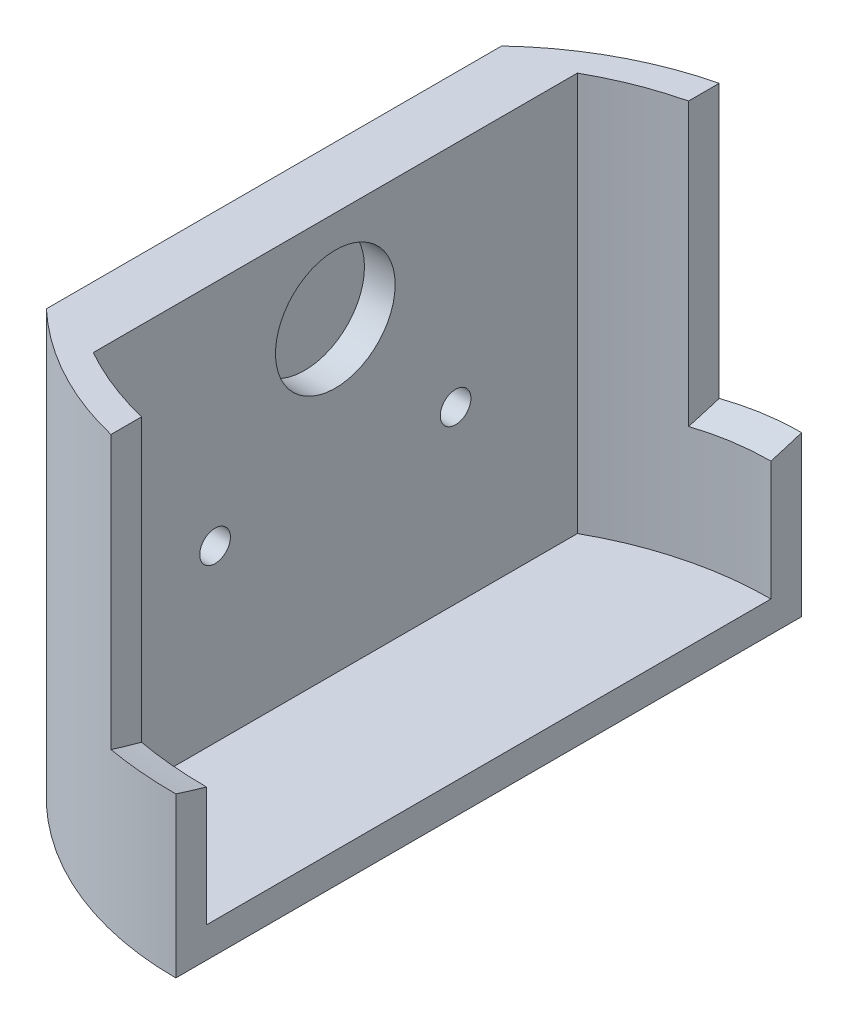
SolidWorks part; units mm, degrees
ref_plane "Plan de face" through (0, 0, 0) normal (0, 0, 1) x (1, 0, 0)
ref_plane "Plan de dessus" through (0, 0, 0) normal (0, 1, 0) x (1, 0, 0)
ref_plane "Plan de droite" through (0, 0, 0) normal (1, 0, 0) x (0, 0, -1)
sketch "Esquisse1" plane through (0, 0, 0) normal (0, 1, 0) x (1, 0, 0)
  line L0 (-50.0182, 0) -> (81.7007, 0) construction
  line L1 (0, 51) -> (0, 46)
  line L4 (0, 46) -> (0, -46)
  line L5 (0, 68.3448) -> (0, -68.3448) construction
  line L10 (0, -46) -> (0, -51)
  line L11 (25, -22.1) -> (25, -17.1)
  line L15 (25, 22.1) -> (25, 17.1)
  line L19 (-25, 39.4522) -> (-25, -39.4522)
  line L20 (-35, 37.0945) -> (-35, -37.0945)
  line L21 (-25, 17.1) -> (25, 17.1)
  line L22 (-25, 22.1) -> (25, 22.1)
  line L23 (-25, -17.1) -> (25, -17.1)
  line L24 (-25, -22.1) -> (25, -22.1)
  arc A0 (-35, -37.0945) -> (0, -51) centre (0, 0) ccw
  arc A1 (0, 51) -> (-35, 37.0945) centre (0, 0) ccw
  arc A4 (-25, 39.4522) -> (0, 46) centre (0, -5) cw
  arc A5 (-25, -39.4522) -> (0, -46) centre (0, 5) ccw
  point P14 (-50, 0)
  point P21 (-18.8011, 42.3964)
  point P22 (-18.8306, 47.3963)
  point P23 (-18.8306, -42.3963)
  point P24 (-18.8306, -47.3963)
  point P33 (25, 19.6)
  point P34 (25, -19.6)
  dimension "D6" = 102
  dimension "D16" = 51
  dimension "D15" = 39.4522
  dimension "D1" = 5
  dimension "D2" = 10
  dimension "D7" = 5
  dimension "D8" = 5
  dimension "D12" = 39.2
  dimension "D13" = 25
  dimension "D14" = 25
extrude "Boss.-Extru.7" add sketch "Esquisse1" along normal mid plane 70
sketch "Esquisse2" plane through (0, -35, 0) normal (0, -1, 0) x (1, 0, 0)
  line L0 (-40.1305, 0) -> (15.1892, 0) construction
  line L1 (-35, 37.0945) -> (-35, -37.0945)
  line L3 (0, 51) -> (0, -51)
  line L4 (-35, -37.0945) -> (-35, 37.0945) construction
  arc A0 (0, 51) -> (-35, 37.0945) centre (0, 0) ccw
  arc A1 (0, 51) -> (-35, 37.0945) centre (0, 0) ccw construction
  arc A2 (0, -51) -> (-35, -37.0945) centre (0, 0) cw
  point P9 (-35, 0)
extrude "Boss.-Extru.8" add sketch "Esquisse2" against normal blind 5
sketch "Esquisse3" plane through (-25, 0, 0) normal (1, 0, 0) x (0, 0, -1)
  line L0 (0, -101.3226) -> (0, -124.5511) construction
  line L1 (85.2632, 80.6789) -> (145.3026, 42.7808)
  line L2 (0, 28.9582) -> (0, -41.9019) construction
  line L3 (-145.3026, 42.7808) -> (-85.2632, 80.6789)
  line L4 (85.2632, 80.6789) -> (145.3026, 42.7808) construction
  line L5 (-51, -35) -> (51, -35) construction
  line L7 (46, -30) -> (-46, -30) construction
  circle A0 centre (-19.6, -2.21) radius 2.5
  circle A1 centre (19.6, -2.21) radius 2.5
  circle A2 centre (0, 146.504) radius 150
  arc A3 (-85.2632, 80.6789) -> (85.2632, 80.6789) centre (0, 125.0981) ccw
  arc A4 (-145.3026, 42.7808) -> (145.3026, 42.7808) centre (0, 125.0981) ccw
  arc A5 (-73.5134, 63.1412) -> (43.9419, 39.5879) centre (0, 125.0981) ccw
  point P6 (0, -3.496)
  point P7 (0, 28.9582)
  point P20 (0, -35)
  dimension "D1" = 300
  dimension "D3" = 5
  dimension "D4" = 167
  dimension "D2" = 39.2
  dimension "D5" = 11.7498
  dimension "D6" = 27.79
extrude "Enlèv. mat.-Extru.1" cut sketch "Esquisse3" against normal blind 5 contours A0 | A1
sketch "Esquisse5" plane through (0, 0, 0) normal (1, 0, 0) x (0, 0, -1)
  line L0 (40.6745, 51.0324) -> (98.0512, 14.8151)
  line L1 (0, 43) -> (0, -17) construction
  line L2 (-98.0512, 14.8151) -> (-40.6745, 51.0324)
  line L3 (40.6745, 51.0324) -> (98.0512, 14.8151) construction
  line L6 (46, -30) -> (-46, -30) construction
  line L7 (51, -35) -> (-51, -35) construction
  arc A0 (-40.6745, 51.0324) -> (40.6745, 51.0324) centre (0, 150) ccw
  arc A1 (-98.0512, 14.8151) -> (98.0512, 14.8151) centre (0, 150) ccw
  arc A3 (-28.9247, 46.9837) -> (27.706, 46.6493) centre (0, 150) ccw
  point P0 (0, 43)
  point P2 (0, -30)
  line M21 (-51, 35) -> (-51, -35)
  line M23 (51, -35) -> (51, 35)
  line M24 (51, 35) -> (46, 35)
  line M25 (46, 35) -> (46, -30)
  line M27 (-46, -30) -> (-46, 35)
  line M28 (-46, 35) -> (-51, 35)
  dimension "D2" = 115.478
  dimension "D3" = 60
  dimension "D7" = 167
  dimension "D4" = 18
  dimension "D10" = 11.7498
extrude "Enlèv. mat.-Extru.2" cut sketch "Esquisse5" against normal blind 12 contours L2 A1 L0 A0 M21 M28 M27 M25 M24 M23 | A1 M21 M27 M28 | A1 M25 M23 M24
sketch "Esquisse6" plane through (-25, 0, 0) normal (1, 0, 0) x (0, 0, -1)
  line L0 (46, -30) -> (-46, -30) construction
  circle A0 centre (0, 20) radius 9.75
  dimension "D1" = 50
  dimension "D2" = 19.5
extrude "Enlèv. mat.-Extru.3" cut sketch "Esquisse6" against normal blind 5
